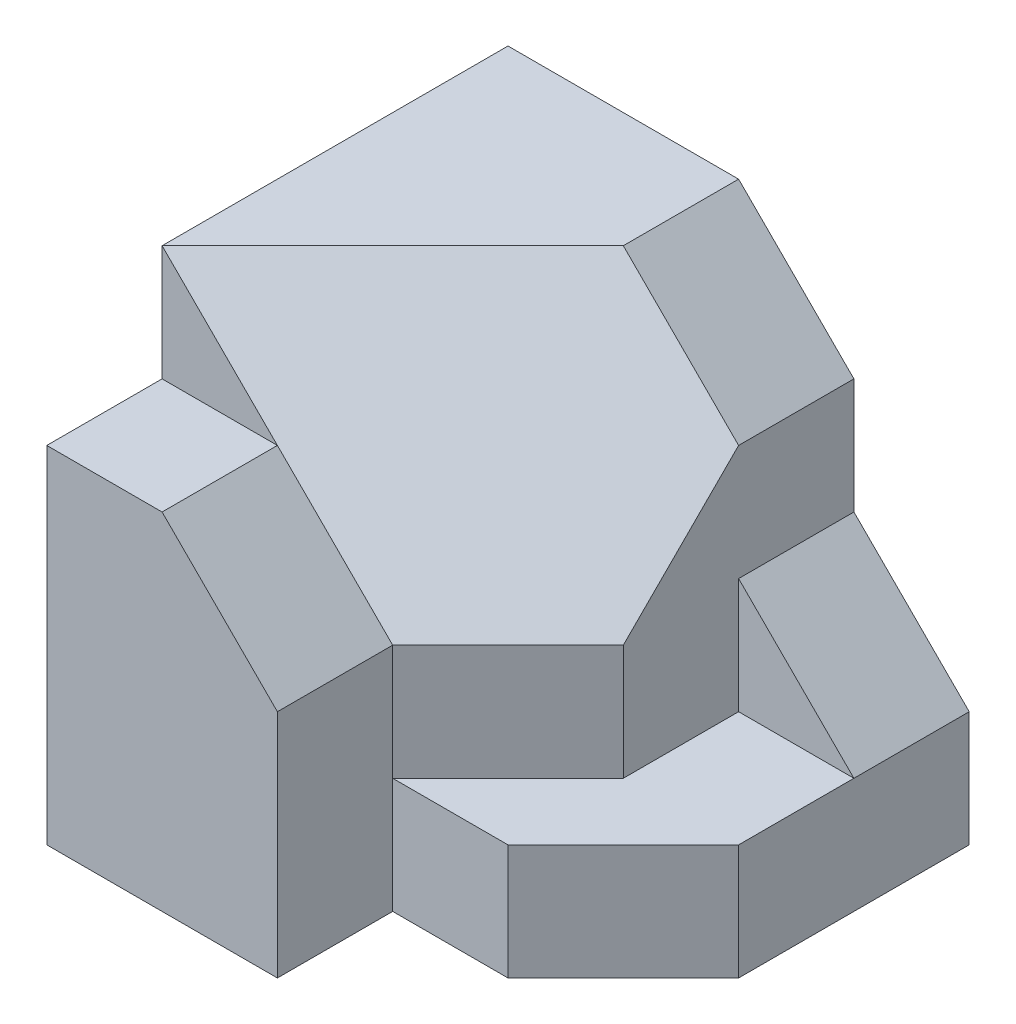
SolidWorks part; units mm, degrees
ref_plane "Front Plane" through (0, 0, 0) normal (0, 0, 1) x (1, 0, 0)
ref_plane "Top Plane" through (0, 0, 0) normal (0, 1, 0) x (1, 0, 0)
ref_plane "Right Plane" through (0, 0, 0) normal (1, 0, 0) x (0, 0, -1)
sketch "Sketch1" plane through (0, 0, 0) normal (0, 1, 0) x (1, 0, 0)
  line L0 (0, -15) -> (0, 0)
  line L1 (0, 0) -> (10, 0)
  line L2 (10, 0) -> (10, -5)
  line L3 (10, -5) -> (0, -15)
  dimension "D1" = 5
  dimension "D2" = 10
  dimension "D3" = 15
extrude "Boss-Extrude1" add sketch "Sketch1" along normal blind 20
sketch "Sketch2" plane through (10, 0, 0) normal (1, 0, 0) x (0, 0, -1)
  line L1 (0, 0) -> (-5, 0)
  line L2 (0, 0) -> (0, 20)
  line L3 (0, 20) -> (-5, 20)
  line L4 (-5, 0) -> (-5, 20)
extrude "Boss-Extrude2" add sketch "Sketch2" along normal blind 5
sketch "Sketch3" plane through (0, 0, 0) normal (0, 0, -1) x (-1, 0, 0)
  line L0 (-10, 20) -> (-15, 20)
  line L1 (-15, 20) -> (0, 20) construction
  line L2 (-15, 20) -> (-15, 15)
  line L3 (-15, 0) -> (-15, 20) construction
  line L4 (-15, 15) -> (-10, 20)
  dimension "D1" = 5
  dimension "D2" = 5
extrude "Cut-Extrude1" cut sketch "Sketch3" against normal blind 21
ref_plane "Plane1" through (0, 0, 0) normal (0, -1, 0) x (-1, 0, 0)
sketch "Sketch4" plane through (0, 0, 0) normal (0, -1, 0) x (-1, 0, 0)
  line L0 (0, -15) -> (-10, -5)
  line L1 (-10, -5) -> (-15, -5)
  line L2 (-15, -5) -> (-15, -10)
  line L3 (-15, -10) -> (-10, -15)
  line L4 (-10, -15) -> (0, -15)
  dimension "D1" = 5
  dimension "D2" = 10
extrude "Boss-Extrude4" add sketch "Sketch4" against normal blind 20
sketch3d "3DSketch1"
  line L0 (10, 20, 5) -> (15, 20, 5) construction
  line L1 (15, 15, 5) -> (10, 20, 5) construction
  line L2 (15, 20, 10) -> (15, 0, 10) construction
  line L3 (10, 20, 15) -> (10, 0, 15) construction
  line L4 (0, 20, 15) -> (10, 20, 5)
  line L5 (10, 20, 5) -> (15, 15, 5)
  line L6 (15, 15, 5) -> (15, 10, 10)
  line L7 (15, 10, 10) -> (10, 10, 15)
  line L8 (10, 10, 15) -> (0, 20, 15)
  point P0 (0, 20, 15)
  point P1 (10, 20, 5)
  point P3 (15, 15, 5)
  point P8 (15, 10, 10)
  point P10 (10, 10, 15)
  dimension "D1" = 10
  dimension "D2" = 10
extrude "Cut-Extrude2" cut sketch "3DSketch1" along direction (1, 0, 0) on the side against the normal blind 70
sketch "Sketch5" plane through (15, 0, 0) normal (1, 0, 0) x (0, 0, -1)
  line L0 (-5, 10) -> (0, 10)
  line L1 (0, 0) -> (0, 15) construction
  line L2 (0, 10) -> (0, 0)
  line L3 (0, 0) -> (-5, 0)
  line L4 (-8.25, 0) -> (8.25, 0) construction
  line L5 (-5, 0) -> (-5, 10)
  dimension "D1" = 5
  dimension "D2" = 10
extrude "Boss-Extrude5" add sketch "Sketch5" along normal blind 5
sketch "Sketch6" plane through (0, 0, 5) normal (0, 0, 1) x (1, 0, 0)
  line L0 (15, 10) -> (20, 5)
  line L1 (20, 10) -> (20, 0) construction
  line L2 (20, 5) -> (20, 10)
  line L3 (20, 10) -> (15, 10)
  dimension "D1" = 5
extrude "Cut-Extrude3" cut sketch "Sketch6" against normal blind 5
sketch "Sketch7" plane through (0, 0, 0) normal (0, -1, 0) x (-1, 0, 0)
  line L0 (-15, -10) -> (-15, -5)
  line L1 (-15, -5) -> (-20, -5)
  line L2 (-20, -5) -> (-20, -10)
  line L3 (-20, -10) -> (-15, -15)
  line L4 (-15, -15) -> (-10, -15)
  line L5 (-15, -10) -> (-10, -15) construction
  line L6 (-10, -15) -> (-15, -10)
  dimension "D1" = 5
extrude "Boss-Extrude6" add sketch "Sketch7" against normal blind 5
sketch "Sketch8" plane through (0, 0, 15) normal (0, 0, 1) x (1, 0, 0)
  line L0 (0, 15) -> (5, 15)
  line L1 (0, 20) -> (0, 0) construction
  line L2 (5, 15) -> (10, 10)
  line L3 (10, 10) -> (10, 0)
  line L4 (-8.25, 0) -> (8.25, 0) construction
  line L5 (10, 0) -> (0, 0)
  line L6 (0, 0) -> (0, 15)
  dimension "D1" = 5
  dimension "D2" = 10
  dimension "D3" = 10
  dimension "D4" = 15
extrude "Boss-Extrude7" add sketch "Sketch8" along normal blind 5
